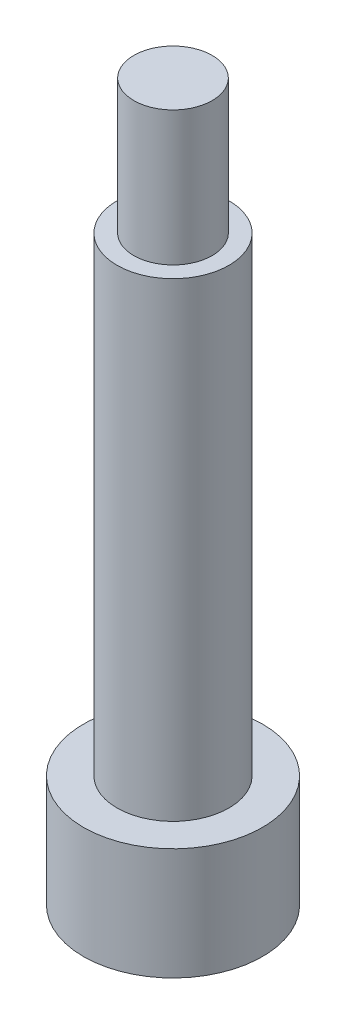
SolidWorks part; units mm, degrees
ref_plane "Front" through (0, 0, 0) normal (0, 0, 1) x (1, 0, 0)
ref_plane "Top" through (0, 0, 0) normal (0, 1, 0) x (1, 0, 0)
ref_plane "Right" through (0, 0, 0) normal (1, 0, 0) x (0, 0, -1)
other "Configuration Table"
sketch "Эскиз1" plane through (0, 0, 0) normal (0, 1, 0) x (1, 0, 0)
  circle A0 centre (0, 0) radius 8
extrude "Бобышка-Вытянуть1" add sketch "Эскиз1" along normal blind 10
sketch "Эскиз2" plane through (0, 10, 0) normal (0, 1, 0) x (1, 0, 0)
  circle A0 centre (0, 0) radius 5
extrude "Бобышка-Вытянуть2" add sketch "Эскиз2" along normal blind 42
sketch "Эскиз3" plane through (0, 52, 0) normal (0, 1, 0) x (1, 0, 0)
  circle A0 centre (0, 0) radius 3.5
extrude "Бобышка-Вытянуть3" add sketch "Эскиз3" along normal blind 12
sketch "Эскиз4" plane through (0, 0, 0) normal (1, 0, 0) x (0, 0, -1)
  line L0 (0, 42) -> (0, 48) construction
  line L1 (-2, 42) -> (-2, 48)
  line L2 (2, 42) -> (2, 48)
  line L3 (5, 52) -> (-5, 52) construction
  arc A0 (-2, 42) -> (2, 42) centre (0, 42) ccw
  arc A1 (2, 48) -> (-2, 48) centre (0, 48) ccw
  point P3 (0, 45)
  dimension "D2" = 10
  dimension "D1" = 4
  dimension "D3" = 4
extrude "Вырез-Вытянуть1" cut sketch "Эскиз4" against normal blind 10
